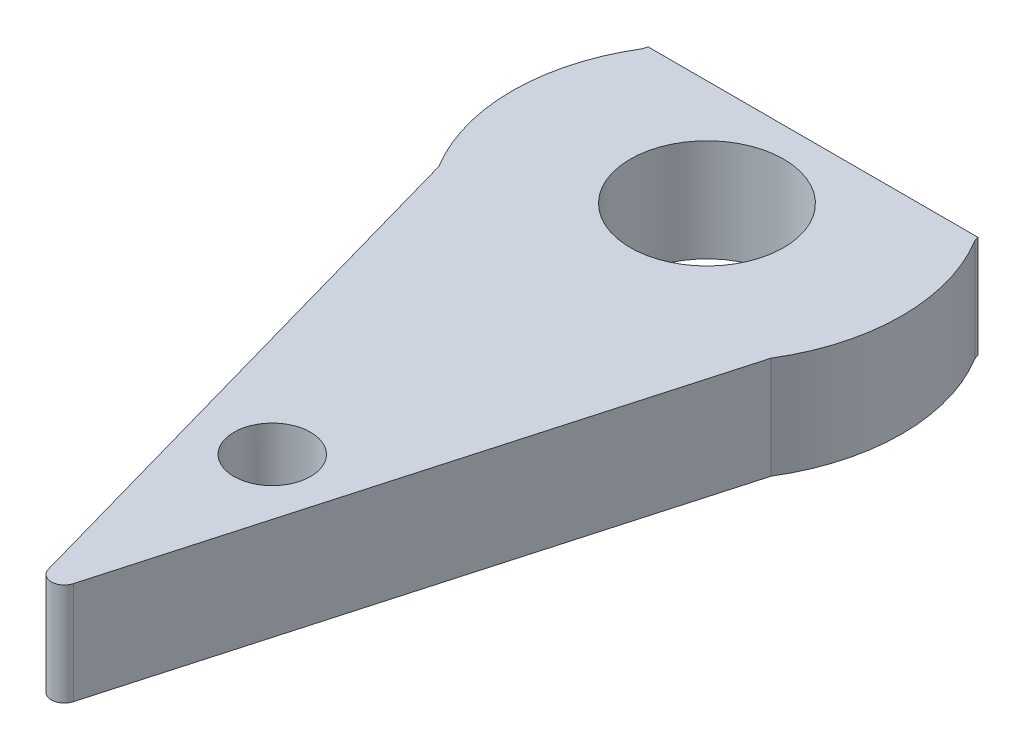
SolidWorks part; units mm, degrees
ref_plane "Front Plane" through (0, 0, 0) normal (0, 0, 1) x (1, 0, 0)
ref_plane "Top Plane" through (0, 0, 0) normal (0, 1, 0) x (1, 0, 0)
ref_plane "Right Plane" through (0, 0, 0) normal (1, 0, 0) x (0, 0, -1)
sketch "Sketch1" plane through (0, 0, 0) normal (0, 1, 0) x (1, 0, 0)
  circle A0 centre (0, 0) radius 3.81
  dimension "D1" = 7.62
extrude "Boss-Extrude1" add sketch "Sketch1" along normal blind 2
sketch "Sketch2" plane through (0, 2, 0) normal (0, 1, 0) x (1, 0, 0)
  line L0 (-3.81, 0) -> (3.81, 0) construction
  line L1 (3.81, 0) -> (0, 13.5)
  line L2 (0, 13.5) -> (-3.81, 0)
  line L3 (0, -13.5) -> (-3.81, 0)
  line L4 (3.81, 0) -> (0, -13.5)
  line L5 (-3.81, 0) -> (3.81, 0)
  circle A0 centre (0, 0) radius 3.81 construction
  circle M2 centre (0, 0) radius 3.81
  dimension "D1" = 27
extrude "Boss-Extrude2" add sketch "Sketch2" against normal up to surface (2 mm away) contours L4 L3 M2 | L1 L2 M2 up to face at (0, 0, 3.81)
fillet "Fillet1" radius 0.254 2 edges at (0, 1, 13.5) (0, 1, -13.5)
sketch "Sketch3" plane through (0, 2, 0) normal (0, 1, 0) x (1, 0, 0)
  line L0 (0, 12.8188) -> (0, -12.8188) construction
  line L1 (-3.81, 0) -> (3.81, 0) construction
  arc A0 (0.2445, 12.6338) -> (-0.2445, 12.6338) centre (0, 12.5648) ccw construction
  arc A1 (-0.2445, -12.6338) -> (0.2445, -12.6338) centre (0, -12.5648) ccw construction
  arc A2 (-3.2478, 1.9919) -> (-3.2478, -1.9919) centre (0, 0) ccw construction
  arc A3 (3.2478, -1.9919) -> (3.2478, 1.9919) centre (0, 0) ccw construction
  circle A4 centre (0, 8.5) radius 0.75
  circle A5 centre (0, -8.5) radius 0.75
  dimension "D1" = 8.5
  dimension "D2" = 1.5
extrude "Cut-Extrude1" cut sketch "Sketch3" against normal up to surface (2 mm away) up to face at (0, 0, 0)
sketch "Sketch4" plane through (0, 0, 0) normal (0, -1, 0) x (1, 0, 0)
  circle A0 centre (0, 0) radius 1.5
  dimension "D1" = 3
extrude "Cut-Extrude2" cut sketch "Sketch4" against normal through all
sketch "Sketch5" plane through (0, 0, 0) normal (0, 1, 0) x (1, 0, 0)
  line L0 (5.4307, 2.0752) -> (-5.9177, 2.0752)
  line L3 (0, 14.8317) -> (5.4307, 14.8317)
  line L4 (5.4307, 2.0752) -> (5.4307, 14.8317)
  line L7 (0, 14.8317) -> (-5.9177, 14.8317)
  line L8 (-5.9177, 2.0752) -> (-5.9177, 14.8317)
extrude "Cut-Extrude3" cut sketch "Sketch5" along normal blind 2.54
